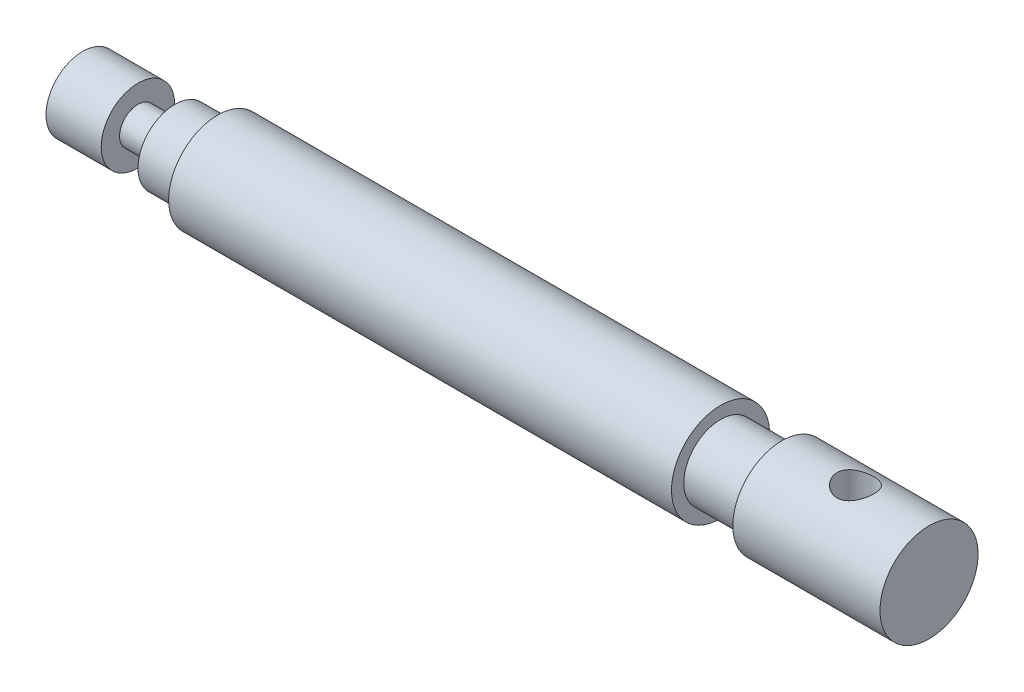
SolidWorks part; units mm, degrees
ref_plane "Front Plane" through (0, 0, 0) normal (0, 0, 1) x (1, 0, 0)
ref_plane "Top Plane" through (0, 0, 0) normal (0, 1, 0) x (1, 0, 0)
ref_plane "Right Plane" through (0, 0, 0) normal (1, 0, 0) x (0, 0, -1)
sketch "Sketch1" plane through (0, 0, 0) normal (0, 1, 0) x (1, 0, 0)
  line L0 (-75.6933, 0) -> (90.0136, 0) construction
  line L1 (-54.7718, 0) -> (-54.7718, 6)
  line L2 (-54.7718, 6) -> (-45.7718, 6)
  line L3 (-45.7718, 6) -> (-45.7718, 3)
  line L4 (-45.7718, 3) -> (-39.7718, 3)
  line L5 (-39.7718, 3) -> (-39.7718, 6)
  line L6 (-39.7718, 6) -> (-32.7718, 6)
  line L7 (-32.7718, 6) -> (-32.7718, 8)
  line L8 (-32.7718, 8) -> (49.2282, 8)
  line L9 (49.2282, 8) -> (49.2282, 6)
  line L10 (49.2282, 6) -> (59.2282, 6)
  line L11 (59.2282, 6) -> (59.2282, 8)
  line L12 (59.2282, 8) -> (83.2282, 8)
  line L13 (83.2282, 8) -> (83.2282, 0)
  line L14 (-54.7718, 0) -> (83.2282, 0)
  dimension "D1" = 138
  dimension "D2" = 9
  dimension "D3" = 6
  dimension "D4" = 3
  dimension "D5" = 6
  dimension "D6" = 8
  dimension "D7" = 24
  dimension "D8" = 8
  dimension "D9" = 10
  dimension "D10" = 82
  dimension "D11" = 6
  dimension "D12" = 7
  dimension "D13" = 6
revolve "Revolve1" add sketch "Sketch1" angle 360 about L14
sketch "Sketch2" plane through (0, 0, 0) normal (0, 0, 1) x (1, 0, 0)
  line L0 (59.4135, 8) -> (83.2282, 8) construction
  line L1 (83.2282, 8) -> (59.2282, 8) construction
  line L3 (83.2282, -8) -> (83.2282, 8) construction
  line L4 (83.2282, -8) -> (83.2282, 8)
ref_plane "Plane1" through (0, 8, 0) normal (0, 1, 0) x (1, 0, 0)
sketch "Sketch3" plane through (0, 8, 0) normal (0, 1, 0) x (1, 0, 0)
  line L0 (83.2282, 0) -> (83.2282, 8) construction
  line L1 (83.2282, -8) -> (83.2282, 8) construction
  line L2 (83.2282, 8) -> (59.2282, 8) construction
  line L3 (59.2282, 8) -> (59.2282, -8) construction
  line L4 (59.2282, -8) -> (83.2282, -8) construction
  line L5 (83.2282, 0) -> (71.2282, 0) construction
  line L6 (59.4135, 0) -> (83.2282, 0) construction
  circle A0 centre (71.2282, 0) radius 3
  dimension "D1" = 12
extrude "Cut-Extrude1" cut sketch "Sketch3" against normal up to next
